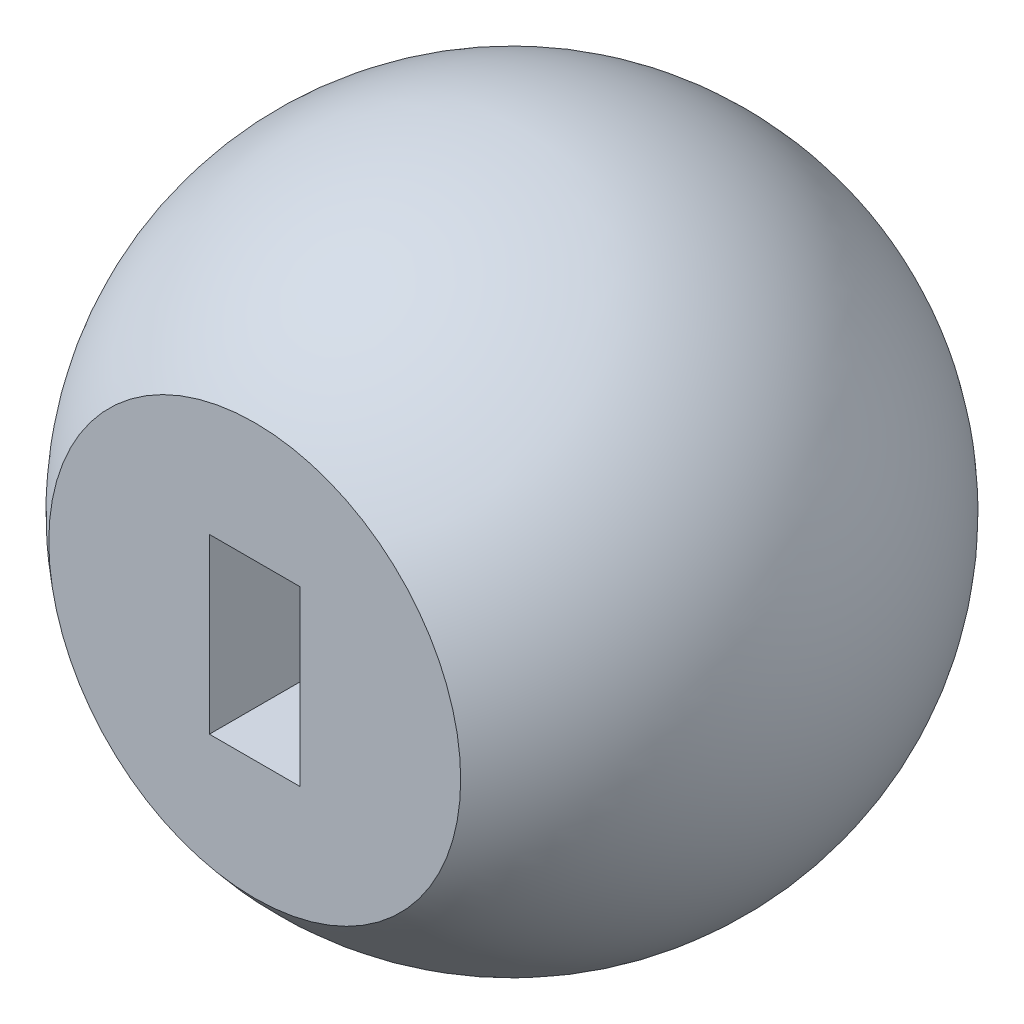
SolidWorks part; units mm, degrees
ref_plane "前视基准面" through (0, 0, 0) normal (0, 0, 1) x (1, 0, 0)
ref_plane "上视基准面" through (0, 0, 0) normal (0, 1, 0) x (1, 0, 0)
ref_plane "右视基准面" through (0, 0, 0) normal (1, 0, 0) x (0, 0, -1)
other "Configuration Table"
sketch "草图1" plane through (0, 0, 0) normal (0, 1, 0) x (1, 0, 0)
  line L1 (-5, -6.245) -> (0, -6.245)
  line L2 (0, -6.245) -> (0, 8)
  arc A2 (0, 8) -> (-5, -6.245) centre (0, 0) ccw
  point P4 (0, 0)
  point P5 (-12.5352, -8.2383)
  point P7 (-10.2532, 6.4207)
  point P9 (-10.2532, 6.4207)
  dimension "D1" = 8
  dimension "D2" = 5
revolve "旋转2" add sketch "草图1" angle 360 about L2
sketch "草图2" plane through (0, 0, 6.245) normal (0, 0, 1) x (1, 0, 0)
  line L1 (-1.1, 2.1) -> (1.1, 2.1)
  line L2 (-1.1, 2.1) -> (-1.1, -2.1)
  line L3 (-1.1, -2.1) -> (1.1, -2.1)
  line L4 (1.1, 2.1) -> (1.1, -2.1)
  line L5 (-1.1, 2.1) -> (1.1, -2.1) construction
  line L6 (-1.1, -2.1) -> (1.1, 2.1) construction
  point P0 (0, 0)
  dimension "D1" = 2.2
  dimension "D2" = 4.2
extrude "切除-拉伸1" cut sketch "草图2" against normal blind 4.2
